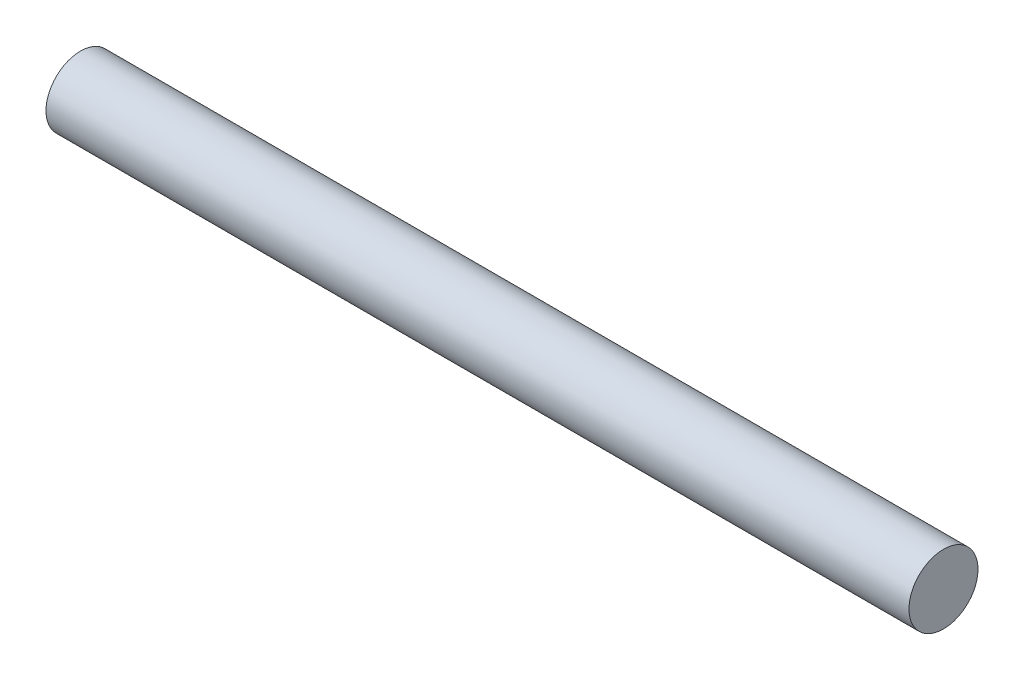
SolidWorks part; units mm, degrees
ref_plane "Front Plane" through (0, 0, 0) normal (0, 0, 1) x (1, 0, 0)
ref_plane "Top Plane" through (0, 0, 0) normal (0, 1, 0) x (1, 0, 0)
ref_plane "Right Plane" through (0, 0, 0) normal (1, 0, 0) x (0, 0, -1)
sketch "Sketch1" plane through (0, 0, 0) normal (0, 0, 1) x (1, 0, 0)
  line L0 (50, 0) -> (-50, 0) construction
  line L1 (-50, 0) -> (-50, 4)
  line L2 (-50, 4) -> (50, 4)
  line L3 (50, 4) -> (50, 0)
  line L4 (-50, 0) -> (50, 0)
  point P4 (0, 0)
  dimension "D1" = 100
  dimension "D2" = 8
revolve "Revolve1" add sketch "Sketch1" angle 360 about L0
